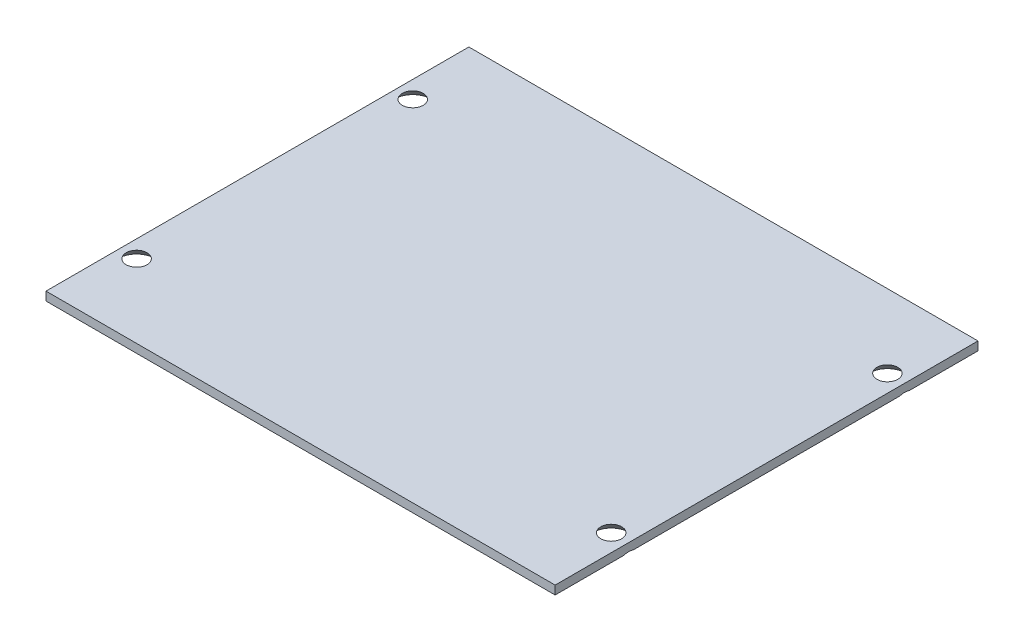
SolidWorks part; units mm, degrees
material "6061-T6 (SS)"
ref_plane "Front Plane" through (0, 0, 0) normal (0, 0, 1) x (1, 0, 0)
ref_plane "Top Plane" through (0, 0, 0) normal (0, 1, 0) x (1, 0, 0)
ref_plane "Right Plane" through (0, 0, 0) normal (1, 0, 0) x (0, 0, -1)
sketch "Sketch1" plane through (0, 0, 0) normal (0, 1, 0) x (1, 0, 0)
  line L1 (-46.8313, 38.8937) -> (46.8312, 38.8937)
  line L2 (-46.8313, 38.8937) -> (-46.8313, -38.8937)
  line L3 (-46.8313, -38.8937) -> (46.8312, -38.8937)
  line L4 (46.8312, 38.8937) -> (46.8312, -38.8937)
  line L5 (-46.8313, 38.8937) -> (46.8312, -38.8937) construction
  line L6 (-46.8313, -38.8937) -> (46.8312, 38.8937) construction
  point P0 (0, 0)
  dimension "D1" = 93.6625
  dimension "D2" = 77.7875
extrude "Boss-Extrude1" add sketch "Sketch1" along normal blind 1.5875
hole_wizard "CSK for #4 Flat Head Machine Screw1" positions "Sketch2" profile "Sketch3" countersink size "#4" standard "ANSI Inch" end condition through all
sketch "Sketch2" plane through (-10.3187, 0, 45.2437) normal (0, -1, 0) x (-1, 0, 0)
  point P0 (-53.975, 70.6437)
  point P3 (-53.975, 19.8438)
  point P6 (33.3375, 19.8438)
  point P9 (33.3375, 70.6438)
sketch "Sketch3" plane through (43.6563, 0, -25.4) normal (1, 0, 0) x (0, 0, -1)
  line L0 (0, 0) -> (0, 1.5875)
  line L1 (0, 1.5875) -> (1.6319, 1.5875)
  line L2 (1.6319, 1.5875) -> (1.6319, 1.9178)
  line L3 (1.6319, 1.9178) -> (3.2991, 0)
  line L4 (3.2991, 0) -> (0, 0)
  line L5 (-1.6319, 1.9178) -> (-3.2991, 0) construction
  line L6 (0, -6.35) -> (0, 107.95) construction
  dimension "Thru Hole Dia." = 3.2639
  dimension "Thru Hole Depth" = 1.5875
  dimension "Near C'Sink Dia." = 6.5982
  dimension "Near C'Sink Angle" = 82
